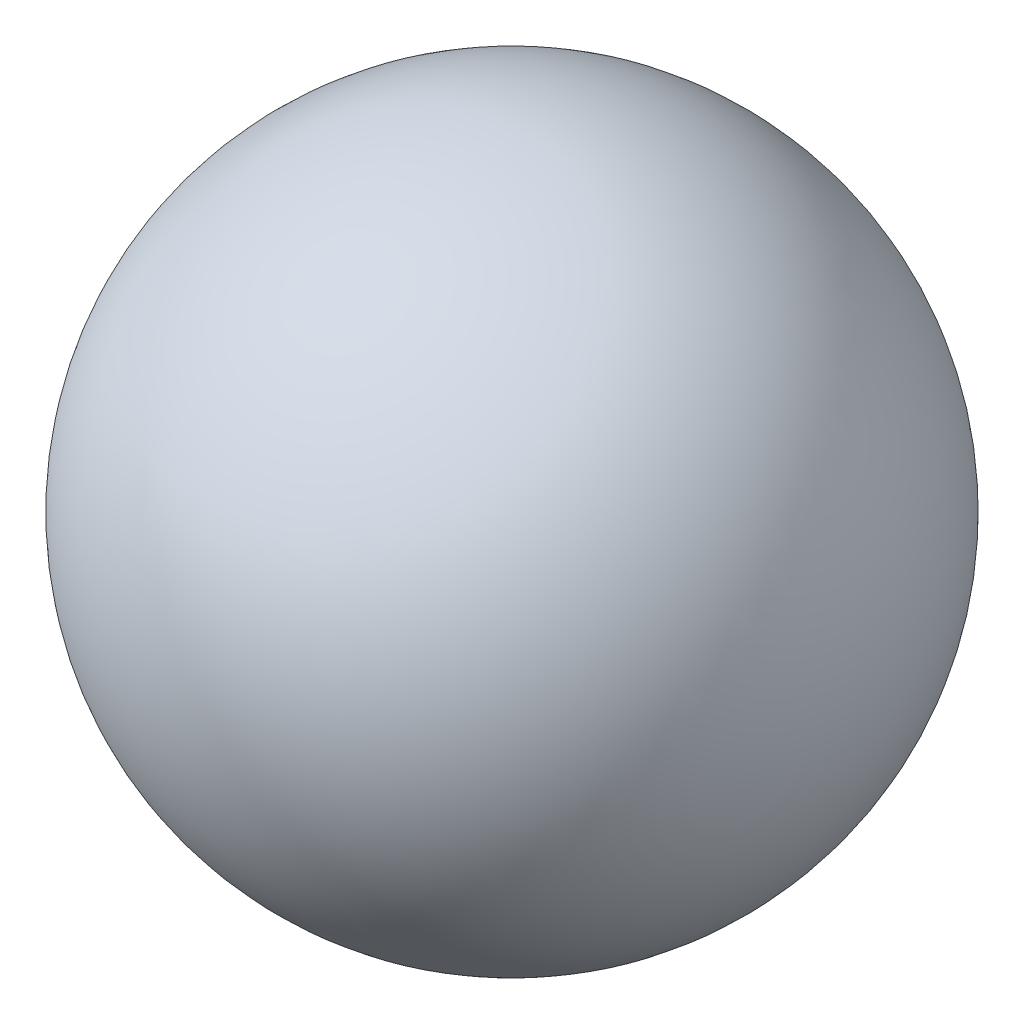
SolidWorks part; units mm, degrees
ref_plane "Front Plane" through (0, 0, 0) normal (0, 0, 1) x (1, 0, 0)
ref_plane "Top Plane" through (0, 0, 0) normal (0, 1, 0) x (1, 0, 0)
ref_plane "Right Plane" through (0, 0, 0) normal (1, 0, 0) x (0, 0, -1)
sketch "Sketch1" plane through (0, 0, 0) normal (0, 0, 1) x (1, 0, 0)
  line L0 (0, -120.65) -> (0, 120.65)
  arc A0 (0, 120.65) -> (0, -120.65) centre (0, 0) cw
  point P4 (0, 0)
  dimension "D2" = 120.65
  dimension "D1" = 241.3
revolve "Revolve1" add sketch "Sketch1" angle 360 about L0
